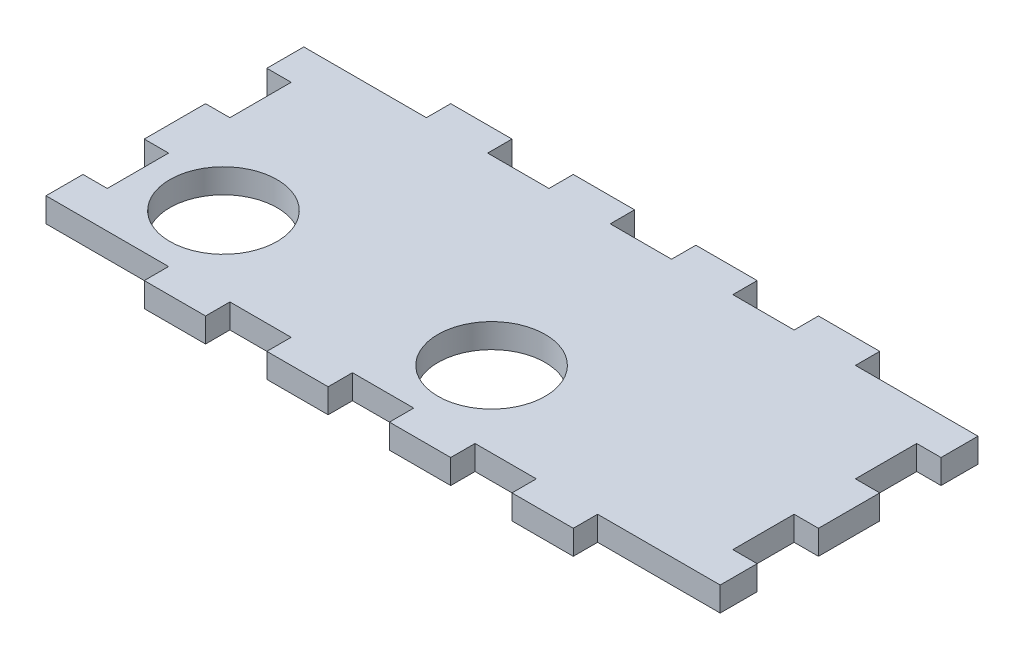
SolidWorks part; units mm, degrees
ref_plane "Front Plane" through (0, 0, 0) normal (0, 0, 1) x (1, 0, 0)
ref_plane "Top Plane" through (0, 0, 0) normal (0, 1, 0) x (1, 0, 0)
ref_plane "Right Plane" through (0, 0, 0) normal (1, 0, 0) x (0, 0, -1)
sketch "Sketch1" plane through (0, 0, 0) normal (0, 1, 0) x (1, 0, 0)
  line L1 (0, 0) -> (88, 0)
  line L2 (0, 0) -> (0, -40)
  line L3 (0, -40) -> (88, -40)
  line L4 (88, 0) -> (88, -40)
  dimension "D1" = 40
  dimension "D2" = 88
extrude "Boss-Extrude1" add sketch "Sketch1" along normal blind 3.175
sketch "Sketch2" plane through (0, 3.175, 0) normal (0, 1, 0) x (1, 0, 0)
  line L0 (44, 0) -> (44, -40) construction
  line L1 (88, 0) -> (0, 0) construction
  line L2 (0, -40) -> (88, -40) construction
  line L3 (0, -20) -> (88, -20) construction
  line L4 (0, 0) -> (0, -40) construction
  line L5 (88, -40) -> (88, 0) construction
  line L6 (16, 0) -> (16, -3.175)
  line L7 (40, 0) -> (48, 0)
  line L8 (0, -3.175) -> (16, -3.175)
  line L9 (40, -3.175) -> (48, -3.175)
  line L10 (48, 0) -> (48, -3.175)
  line L11 (56, 0) -> (64, 0)
  line L12 (56, 0) -> (56, -3.175)
  line L13 (56, -3.175) -> (64, -3.175)
  line L14 (64, 0) -> (64, -3.175)
  line L15 (88, 0) -> (72, 0)
  line L16 (88, 0) -> (88, -3.175)
  line L17 (88, -3.175) -> (72, -3.175)
  line L18 (72, 0) -> (72, -3.175)
  line L19 (0, 0) -> (0, -3.175)
  line L20 (0, 0) -> (16, 0)
  line L21 (24, 0) -> (24, -3.175)
  line L22 (32, -3.175) -> (24, -3.175)
  line L23 (32, 0) -> (32, -3.175)
  line L24 (32, 0) -> (24, 0)
  line L25 (40, 0) -> (40, -3.175)
  line L26 (40, -40) -> (40, -36.825)
  line L27 (32, -40) -> (24, -40)
  line L28 (32, -40) -> (32, -36.825)
  line L29 (32, -36.825) -> (24, -36.825)
  line L30 (24, -40) -> (24, -36.825)
  line L31 (0, -40) -> (16, -40)
  line L32 (0, -40) -> (0, -36.825)
  line L33 (72, -40) -> (72, -36.825)
  line L34 (88, -36.825) -> (72, -36.825)
  line L35 (88, -40) -> (88, -36.825)
  line L36 (88, -40) -> (72, -40)
  line L37 (64, -40) -> (64, -36.825)
  line L38 (56, -36.825) -> (64, -36.825)
  line L39 (56, -40) -> (56, -36.825)
  line L40 (56, -40) -> (64, -40)
  line L41 (48, -40) -> (48, -36.825)
  line L42 (40, -36.825) -> (48, -36.825)
  line L43 (0, -36.825) -> (16, -36.825)
  line L44 (40, -40) -> (48, -40)
  line L45 (16, -40) -> (16, -36.825)
  point P34 (44, -3.175)
  point P54 (44, -36.825)
  dimension "D1" = 4
  dimension "D2" = 3.175
  dimension "D3" = 3.175
  dimension "D4" = 8
  dimension "D5" = 8
  dimension "D6" = 3.175
  dimension "D7" = 8
extrude "Cut-Extrude1" cut sketch "Sketch2" against normal up to next
sketch "Sketch3" plane through (0, 3.175, 0) normal (0, 1, 0) x (1, 0, 0)
  line L0 (0, -20) -> (88, -20) construction
  line L1 (0, -3.175) -> (0, -36.825) construction
  line L2 (88, -36.825) -> (88, -3.175) construction
  line L3 (3.175, -24) -> (3.175, -32)
  line L4 (0, -16) -> (3.175, -16)
  line L5 (0, -16) -> (0, -8)
  line L6 (0, -8) -> (3.175, -8)
  line L7 (3.175, -16) -> (3.175, -8)
  line L8 (0, -32) -> (3.175, -32)
  line L9 (0, -24) -> (0, -32)
  line L10 (0, -24) -> (3.175, -24)
  line L11 (44, -3.175) -> (44, -36.825) construction
  line L12 (40, -3.175) -> (48, -3.175) construction
  line L13 (48, -36.825) -> (40, -36.825) construction
  line L14 (88, -24) -> (84.825, -24)
  line L15 (88, -24) -> (88, -32)
  line L16 (88, -32) -> (84.825, -32)
  line L17 (84.825, -16) -> (84.825, -8)
  line L18 (88, -8) -> (84.825, -8)
  line L19 (88, -16) -> (88, -8)
  line L20 (88, -16) -> (84.825, -16)
  line L21 (84.825, -24) -> (84.825, -32)
  dimension "D1" = 8
  dimension "D2" = 3.175
  dimension "D3" = 4
extrude "Cut-Extrude2" cut sketch "Sketch3" against normal up to next
sketch "Sketch4" plane through (0, 3.175, 0) normal (0, 1, 0) x (1, 0, 0)
  line L0 (0, -16) -> (0, -24) construction
  line L1 (16, -36.825) -> (0, -36.825) construction
  circle A0 centre (13.25, -26.915) radius 7
  circle A1 centre (48.25, -26.915) radius 7
  dimension "D1" = 14
  dimension "D2" = 13.25
  dimension "D4" = 35
  dimension "D5" = 9.91
  dimension "D3" = 2
extrude "Cut-Extrude3" cut sketch "Sketch4" against normal up to next
